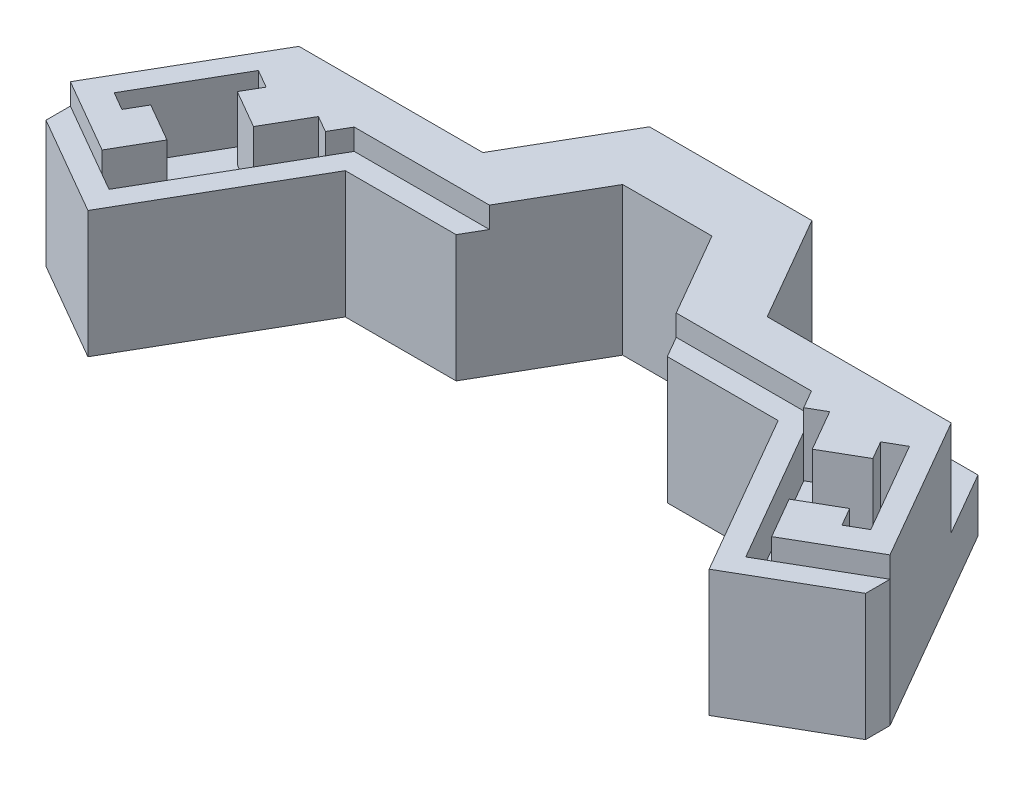
SolidWorks part; units mm, degrees
ref_plane "Front Plane" through (0, 0, 0) normal (0, 0, 1) x (1, 0, 0)
ref_plane "Top Plane" through (0, 0, 0) normal (0, 1, 0) x (1, 0, 0)
ref_plane "Right Plane" through (0, 0, 0) normal (1, 0, 0) x (0, 0, -1)
sketch "Sketch2" plane through (0, 0, 0) normal (0, 1, 0) x (1, 0, 0)
  line L0 (-21.65, 0) -> (0, 0)
  line L1 (-21.65, 0) -> (-30.15, -14.7224)
  line L2 (0, 0) -> (0, 30.0471) construction
  line L3 (-30.15, -14.7224) -> (-38.8103, -9.7224)
  line L4 (-38.8103, -9.7224) -> (-27.4235, 10)
  line L5 (-27.4235, 10) -> (0, 10)
  line L6 (0, 0) -> (0, 10)
  point P2 (0, 0)
  point P9 (-1.8466, 0)
  point P10 (0, 0)
  dimension "D1" = 21.65
  dimension "D2" = 120
  dimension "D3" = 17
  dimension "D4" = 10
  dimension "D5" = 10
extrude "Boss-Extrude1" add sketch "Sketch2" along normal blind 14
sketch "Sketch5" plane through (0, 0, 0) normal (0, 1, 0) x (1, 0, 0)
  line L0 (-38.8103, -9.7224) -> (-38.8103, -12.0318)
  line L1 (-38.8103, -12.0318) -> (-29.4179, -17.4545)
  line L2 (-29.4179, -17.4545) -> (-20.4953, -2)
  line L3 (-20.4953, -2) -> (0, -2)
  line L4 (0, -2) -> (0, 0)
  line L5 (-38.8103, -9.7224) -> (-30.15, -14.7224) construction
  line L6 (-30.15, -14.7224) -> (-21.65, 0) construction
  line L7 (-21.65, 0) -> (0, 0) construction
  line L8 (-38.8103, -9.7224) -> (-30.15, -14.7224)
  line L9 (-30.15, -14.7224) -> (-21.65, 0)
  line L10 (-21.65, 0) -> (0, 0)
  point P5 (-38.8103, -11.8439)
  dimension "D1" = 2
  dimension "D2" = 2
  dimension "D3" = 2
extrude "Boss-Extrude2" add sketch "Sketch5" along normal blind 12
sketch "Sketch6" plane through (0, 14, 0) normal (0, 1, 0) x (1, 0, 0)
  line L18 (-30.15, -14.7224) -> (-31.7088, -13.8224)
  line L19 (-31.7088, -13.8224) -> (-29.4588, -9.9253)
  line L20 (-24.2088, -0.8321) -> (-22.65, -1.7321)
  line L22 (-22.65, -1.7321) -> (-30.15, -14.7224)
  line L23 (-21.65, 0) -> (-30.15, -14.7224) construction
  line L25 (-34.0962, -9.5574) -> (-35.8282, -8.5574)
  line L26 (-35.8282, -8.5574) -> (-30.8282, 0.1029)
  line L27 (-30.8282, 0.1029) -> (-29.0962, -0.8971)
  line L28 (-29.0962, -0.8971) -> (-30.0962, -2.6292)
  line L29 (-30.15, -14.7224) -> (-38.8103, -9.7224) construction
  line L30 (-30.15, -14.7224) -> (-21.65, 0) construction
  line L31 (-27.4235, 10) -> (-38.8103, -9.7224) construction
  line L32 (-33.0962, -7.8253) -> (-29.4588, -9.9253)
  line L33 (-30.0962, -2.6292) -> (-26.4588, -4.7292)
  line L34 (-33.0962, -7.8253) -> (-34.0962, -9.5574)
  line L35 (-26.4588, -4.7292) -> (-24.2088, -0.8321)
  dimension "D1" = 1.8
  dimension "D2" = 15
  dimension "D3" = 10
  dimension "D4" = 2
  dimension "D5" = 2
  dimension "D6" = 6
extrude "Cut-Extrude2" cut sketch "Sketch6" against normal blind 6
sketch "Sketch7" plane through (0, 14, 0) normal (0, 1, 0) x (1, 0, 0)
  line L0 (-21.65, 0) -> (0, 0) construction
  line L1 (3.6811, 4) -> (-35.3509, 4)
  line L2 (3.6811, 4) -> (3.6811, 12.1481)
  line L3 (3.6811, 12.1481) -> (-35.3509, 12.1481)
  line L4 (-35.3509, 4) -> (-35.3509, 12.1481)
  dimension "D1" = 4
extrude "Cut-Extrude3" cut sketch "Sketch7" against normal blind 9
mirror "Mirror2" about plane through (0, 0, 0) normal (1, 0, 0) of "Boss-Extrude1", "Boss-Extrude2", "Cut-Extrude2", "Cut-Extrude3"
sketch "Sketch8" plane through (0, 14, 0) normal (0, 1, 0) x (1, 0, 0)
  line L0 (-10, -2) -> (-4.2265, 8)
  line L1 (-20.4953, -2) -> (20.4953, -2) construction
  line L2 (-4.2265, 8) -> (4.2265, 8)
  line L3 (4.2265, 8) -> (10, -2)
  line L4 (10, -2) -> (-10, -2)
  point P4 (7.4202, -2)
  point P7 (0, -2)
  dimension "D1" = 120
  dimension "D2" = 120
  dimension "D3" = 20
  dimension "D4" = 10
extrude "Cut-Extrude4" cut sketch "Sketch8" against normal up to surface (14 mm away) up to face at (0, 0, 6.2417)
sketch "Sketch9" plane through (0, 14, 0) normal (0, 1, 0) x (1, 0, 0)
  line L0 (-13.4641, 4) -> (-7.6906, 14)
  line L1 (-6.5359, 4) -> (-30.8876, 4) construction
  line L2 (-7.6906, 14) -> (7.6906, 14)
  line L3 (7.6906, 14) -> (13.4641, 4)
  line L4 (6.5359, 4) -> (30.8876, 4) construction
  line L5 (13.4641, 4) -> (6.5359, 4)
  line L6 (6.5359, 4) -> (4.2265, 8) construction
  line L7 (6.5359, 4) -> (4.2265, 8)
  line L8 (4.2265, 8) -> (-4.2265, 8)
  line L9 (-4.2265, 8) -> (-6.5359, 4)
  line L10 (-6.5359, 4) -> (-13.4641, 4)
  point P4 (-4.2265, 8)
  point P18 (-12.0877, 4)
  dimension "D2" = 120
  dimension "D3" = 6
  dimension "D5" = 6
extrude "Boss-Extrude3" add sketch "Sketch9" against normal up to surface (14 mm away) up to face at (0, 0, 3.6012)
